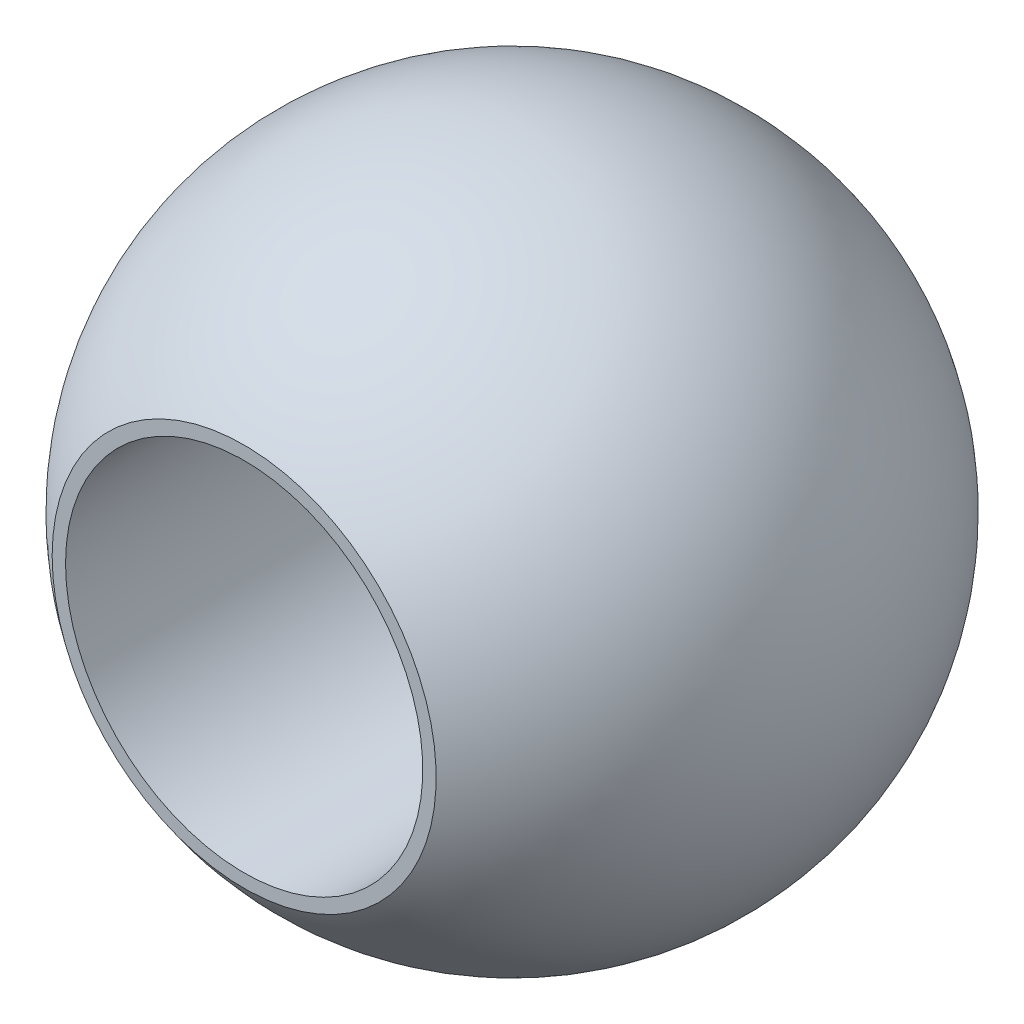
SolidWorks part; units mm, degrees
material "Stainless Steel (ferritic)"
ref_plane "Front Plane" through (0, 0, 0) normal (0, 0, 1) x (1, 0, 0)
ref_plane "Top Plane" through (0, 0, 0) normal (0, 1, 0) x (1, 0, 0)
ref_plane "Right Plane" through (0, 0, 0) normal (1, 0, 0) x (0, 0, -1)
sketch "Sketch1" plane through (0, 0, 0) normal (0, 1, 0) x (1, 0, 0)
  line L0 (4, 6) -> (4, -6)
  line L1 (0, 0) -> (0, -11.0212) construction
  line L2 (4, 6) -> (4.3, 6)
  line L3 (4.3, -6) -> (4, -6)
  arc A1 (4.3, -6) -> (4.3, 6) centre (0, 0) ccw
  point P2 (4, 0)
  dimension "D1" = 12
  dimension "D2" = 4
  dimension "D3" = 0.3
revolve "Revolve1" add sketch "Sketch1" angle 360 about L1
